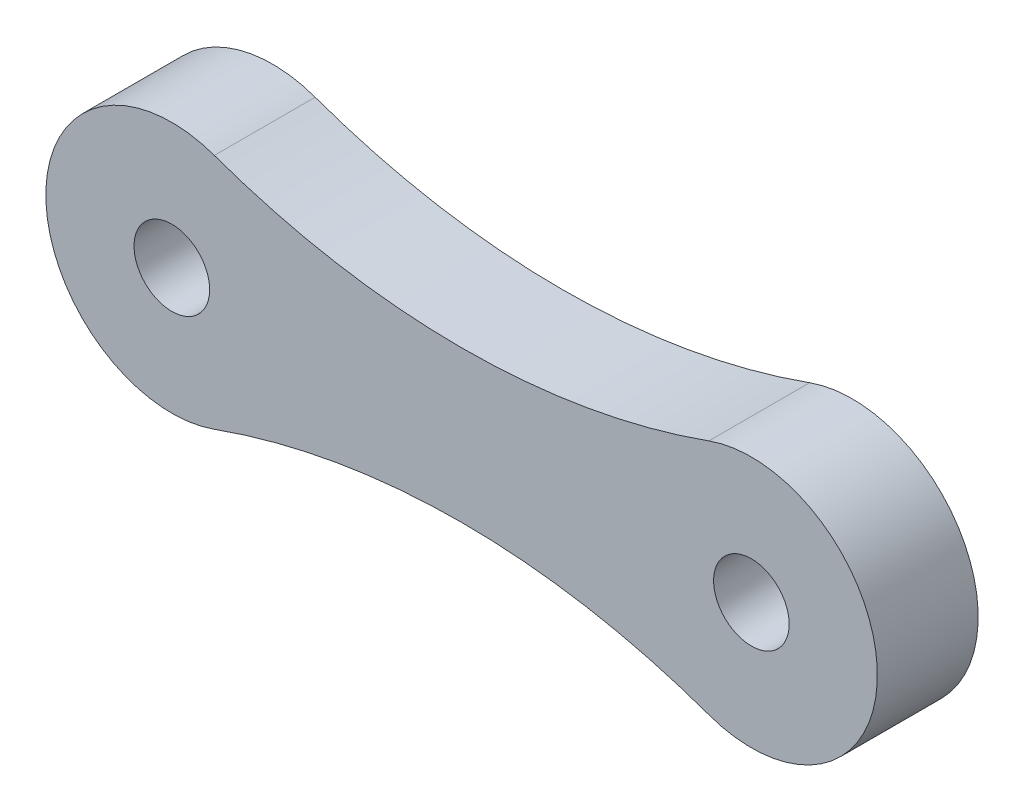
SolidWorks part; units mm, degrees
material "ABS"
ref_plane "Front Plane" through (0, 0, 0) normal (0, 0, 1) x (1, 0, 0)
ref_plane "Top Plane" through (0, 0, 0) normal (0, 1, 0) x (1, 0, 0)
ref_plane "Right Plane" through (0, 0, 0) normal (1, 0, 0) x (0, 0, -1)
sketch "Sketch1" plane through (0, 0, 0) normal (0, 0, 1) x (1, 0, 0)
  line L0 (0, 0) -> (0, 8.5585) construction
  line L1 (-5.75, 0) -> (5.75, 0) construction
  circle A0 centre (-5.75, 0) radius 2.5
  circle A1 centre (5.75, 0) radius 2.5
  arc A2 (-4.906, 2.3532) -> (4.906, 2.3532) centre (0, 16.0312) ccw
  arc A3 (-4.906, -2.3532) -> (4.906, -2.3532) centre (0, -16.0312) cw
  circle A4 centre (-5.75, 0) radius 0.75
  circle A5 centre (5.75, 0) radius 0.75
  point P13 (0, 1.5)
  point P14 (0, -1.5)
  dimension "D1" = 5
  dimension "D3" = 3
  dimension "D4" = 1.5
  dimension "D2" = 5.75
extrude "Boss-Extrude1" add sketch "Sketch1" along normal blind 2 contours A0 A4 | A0 A3 A1 A2 | A1 A5
